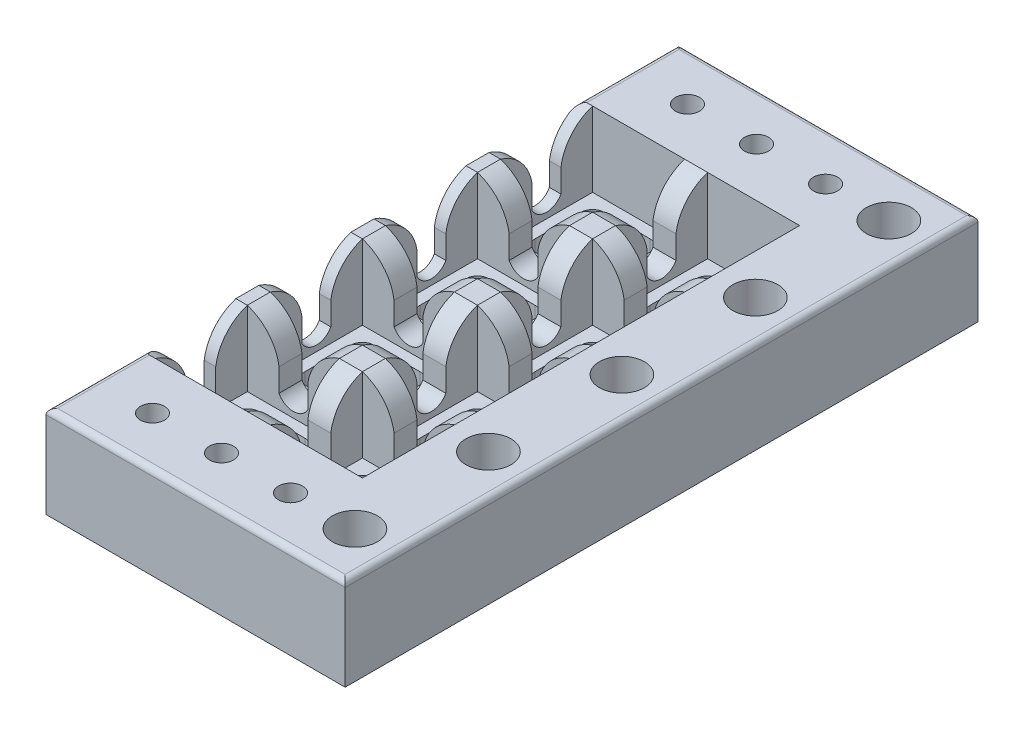
SolidWorks part; units mm, degrees
ref_plane "Front Plane" through (0, 0, 0) normal (0, 0, 1) x (1, 0, 0)
ref_plane "Top Plane" through (0, 0, 0) normal (0, 1, 0) x (1, 0, 0)
ref_plane "Right Plane" through (0, 0, 0) normal (1, 0, 0) x (0, 0, -1)
sketch "Sketch2" plane through (0, 0, 0) normal (0, 1, 0) x (1, 0, 0)
  line L0 (-7.62, -5.08) -> (-7.62, 5.08)
  line L1 (-12.7, -12.7) -> (12.7, -12.7)
  line L2 (-12.7, -12.7) -> (-12.7, 12.7)
  line L3 (-12.7, 12.7) -> (12.7, 12.7)
  line L4 (12.7, -12.7) -> (12.7, 12.7)
  line L5 (-12.7, -12.7) -> (12.7, 12.7) construction
  line L6 (-12.7, 12.7) -> (12.7, -12.7) construction
  line L7 (-5.08, 7.62) -> (5.08, 7.62)
  line L8 (7.62, -5.08) -> (7.62, 5.08)
  line L9 (-5.08, -7.62) -> (5.08, -7.62)
  line L10 (-7.62, -7.62) -> (-7.62, 7.62) construction
  line L11 (-7.62, -7.62) -> (7.62, -7.62) construction
  line L12 (7.62, -7.62) -> (7.62, 7.62) construction
  line L13 (-7.62, 7.62) -> (7.62, 7.62) construction
  arc A2 (-7.62, -5.08) -> (-5.08, -7.62) centre (-5.08, -5.08) ccw
  arc A3 (7.62, -5.08) -> (5.08, -7.62) centre (5.08, -5.08) cw
  arc A4 (5.08, 7.62) -> (7.62, 5.08) centre (5.08, 5.08) cw
  arc A5 (-7.62, 5.08) -> (-5.08, 7.62) centre (-5.08, 5.08) cw
  point P0 (6.8761, -6.8761)
  dimension "D1" = 25.4
  dimension "D4" = 2.54
  dimension "D5" = 9.7242
  dimension "D2" = 25.4
  dimension "D6" = 17.9605
  dimension "D3" = 5.08
extrude "Boss-Extrude1" add sketch "Sketch2" along normal blind 5.08
sketch "Sketch3" plane through (0, 0, -12.7) normal (0, 0, -1) x (-1, 0, 0)
  line L0 (12.7, 5.08) -> (12.7, 0) construction
  line L1 (-12.7, 5.08) -> (12.7, 5.08)
  line L2 (-12.7, 5.08) -> (-12.7, 21.59)
  line L3 (-12.7, 21.59) -> (12.7, 21.59)
  line L4 (12.7, 5.08) -> (12.7, 21.59)
  line L5 (-12.7, 13.335) -> (12.7, 13.335) construction
  line L6 (0, 21.59) -> (0, 0) construction
  line L7 (-12.7, 0) -> (12.7, 0) construction
  line L8 (-3.175, 13.335) -> (-3.175, 5.08)
  line L9 (3.175, 13.335) -> (3.175, 5.08)
  arc A0 (-10.16, 21.59) -> (-3.175, 13.335) centre (-13.234, 11.9062) cw
  arc A1 (10.16, 21.59) -> (3.175, 13.335) centre (13.234, 11.9062) ccw
  arc A2 (-3.175, 8.255) -> (3.175, 8.255) centre (0, 9.9483) ccw
  point P24 (0, 6.35)
  dimension "D1" = 16.51
  dimension "D2" = 6.35
  dimension "D3" = 2.54
  dimension "D4" = 10.16
  dimension "D5" = 5.08
  dimension "D6" = 5.08
  dimension "D7" = 6.35
extrude "Boss-Extrude2" add sketch "Sketch3" against normal blind 2.54
ref_plane "Plane1" through (0, 0, 0) normal (-0.7071, 0, -0.7071) x (-0.7071, 0, 0.7071)
mirror "Mirror4" about plane through (0, 0, 0) normal (0, 0, 1) of "Boss-Extrude2"
mirror "Mirror5" about plane through (0, 0, 0) normal (-0.7071, 0, -0.7071) of "Mirror4", "Boss-Extrude2"
pattern_linear "LPattern1" count 2 spacing 25.4 along (1, 0, 0) count 4 spacing 25.4 along (0, 0, -1) of bodies 107
combine bodies "Combine1" operation type add bodies to combine 108 109 110 111 112 113 107 114
sketch "Sketch6" plane through (0, 0, 0) normal (0, 1, 0) x (1, 0, 0)
  line L0 (-12.7, 88.9) -> (-12.7, 107.95)
  line L1 (-12.7, 107.95) -> (53.34, 107.95)
  line L2 (53.34, 107.95) -> (53.34, -31.75)
  line L3 (53.34, -31.75) -> (-12.7, -31.75)
  line L4 (-12.7, -31.75) -> (-12.7, -12.7)
  line L6 (-12.7, -12.7) -> (38.1, -12.7) construction
  line L7 (38.1, -12.7) -> (38.1, 88.9) construction
  line L8 (38.1, 88.9) -> (-12.7, 88.9) construction
  line L9 (-12.7, -12.7) -> (38.1, -12.7)
  line L10 (38.1, -12.7) -> (38.1, 88.9)
  line L11 (38.1, 88.9) -> (-12.7, 88.9)
  line L12 (-12.7, -10.16) -> (35.56, -10.16)
  line L13 (35.56, -10.16) -> (35.56, 86.36)
  line L14 (35.56, 86.36) -> (-12.7, 86.36)
  line L15 (-12.7, -10.16) -> (-12.7, -12.7)
  line L16 (-12.7, 88.9) -> (-12.7, 86.36)
  dimension "D1" = 66.04
  dimension "D2" = 139.7
  dimension "D3" = 2.54
extrude "Boss-Extrude4" add sketch "Sketch6" along normal blind 21.59 contours L11 L10 L9 L4 L3 L2 L1 L0 | L11 L16 L14 L13 L12 L15 L9 L10
sketch "Sketch9" plane through (0, 21.59, 0) normal (0, 1, 0) x (1, 0, 0)
  line L0 (-12.7, 97.155) -> (53.34, 97.155) construction
  line L1 (-12.7, 86.36) -> (-12.7, 107.95) construction
  line L2 (53.34, 107.95) -> (53.34, -31.75) construction
  line L3 (-12.7, -20.955) -> (53.34, -20.955) construction
  line L4 (-12.7, -31.75) -> (-12.7, -10.16) construction
  line L5 (44.45, 97.155) -> (44.45, -20.955) construction
  line L6 (44.45, 38.1) -> (53.34, 38.1) construction
  dimension "D1" = 8.89
ref_plane "Plane2" through (0, 0, -97.155) normal (0, 0, 1) x (1, 0, 0)
sketch "Sketch10" plane through (0, 0, -97.155) normal (0, 0, 1) x (1, 0, 0)
  line L0 (0, 11.1478) -> (0, 21.59)
  line L1 (-12.7, 21.59) -> (53.34, 21.59) construction
  line L2 (0, 11.1478) -> (2.6586, 13.3423)
  line L3 (2.6586, 13.3423) -> (2.6586, 21.59)
  line L4 (2.6586, 21.59) -> (0, 21.59)
revolve "Cut-Revolve1" cut sketch "Sketch10" angle 360 about L0
pattern_linear "LPattern2" count 3 spacing 15.24 along (1, 0, 0) count 2 spacing 118.11 along (0, 0, 1) of "Cut-Revolve1"
ref_plane "Plane3" through (44.45, 0, 0) normal (-1, 0, 0) x (0, 0, 1)
sketch "Sketch11" plane through (44.45, 0, 0) normal (-1, 0, 0) x (0, 0, 1)
  line L0 (-97.155, 21.59) -> (-97.155, 9.533)
  line L1 (-97.155, 9.533) -> (-92.1795, 12.6636)
  line L2 (-92.1795, 12.6636) -> (-92.1795, 21.59)
  line L3 (-97.155, 21.59) -> (20.955, 21.59) construction
  line L4 (-92.1795, 21.59) -> (-97.155, 21.59)
revolve "Cut-Revolve2" cut sketch "Sketch11" angle 360 about L0
pattern_linear "LPattern3" count 5 spacing 29.464 along (0, 0, 1) of "Cut-Revolve2"
chamfer "Chamfer1" distance 1.27 angle 45 4 edges at (-12.7, 0, -38.1) (20.32, 0, -107.95) (53.34, 0, -38.1) (20.32, 0, 31.75)
fillet "Fillet1" radius 1.27 5 edges at (-12.7, 21.59, -97.155) (-12.7, 21.59, 20.955) (20.32, 21.59, 31.75) (53.34, 21.59, -38.1) (20.32, 21.59, -107.95)
sketch "Sketch12" plane through (-12.7, 0, 0) normal (-1, 0, 0) x (0, 0, 1)
  text T0 "CILS" font "Sitka Subheading" height 7.62
extrude "Cut-Extrude1" cut sketch "Sketch12" against normal blind 1.27
